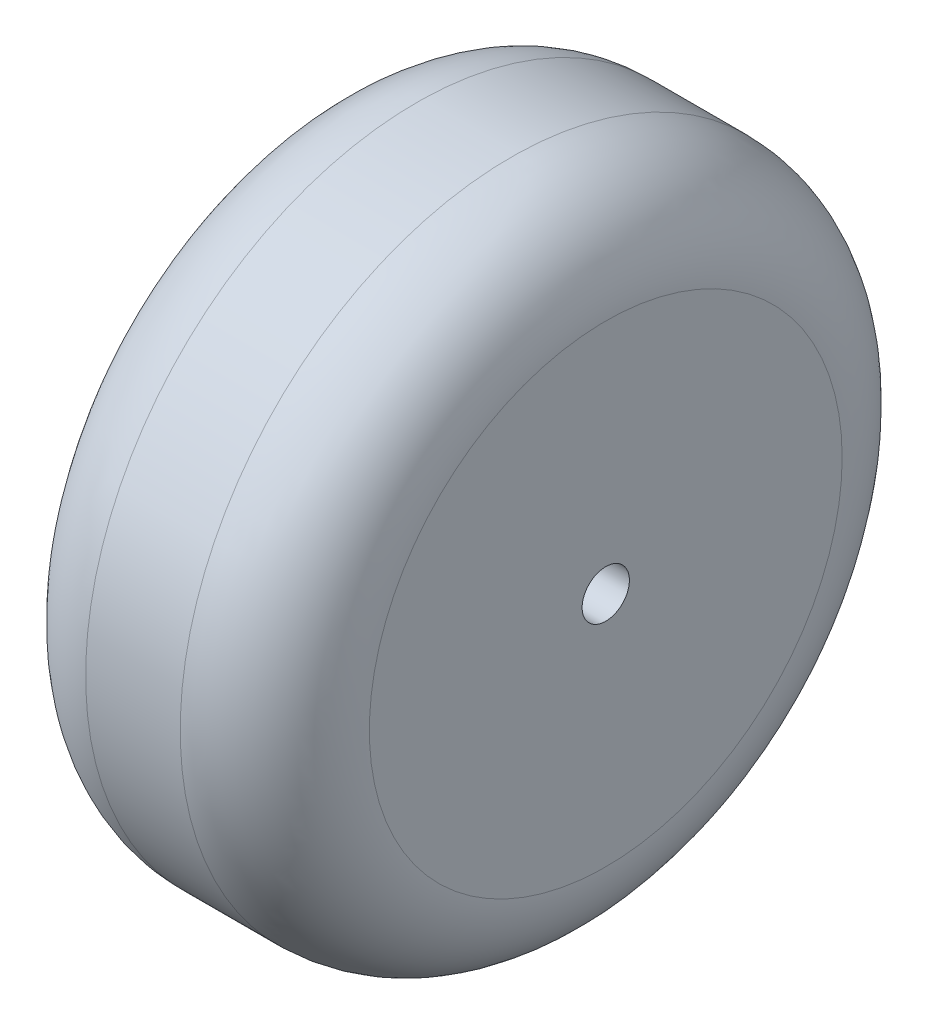
SolidWorks part; units mm, degrees
material "Силиконовая резина"
ref_plane "Спереди" through (0, 0, 0) normal (0, 0, 1) x (1, 0, 0)
ref_plane "Сверху" through (0, 0, 0) normal (0, 1, 0) x (1, 0, 0)
ref_plane "Справа" through (0, 0, 0) normal (1, 0, 0) x (0, 0, -1)
sketch "Эскиз1" plane through (0, 0, 0) normal (1, 0, 0) x (0, 0, -1)
  circle A0 centre (0, 0) radius 35
  circle A1 centre (0, 0) radius 2.5
  dimension "D1" = 70
  dimension "D2" = 5
extrude "колесо" add sketch "Эскиз1" along normal blind 30
fillet "Скругление2" radius 10 2 edges at (30, 0, -35) (0, 0, -35)
